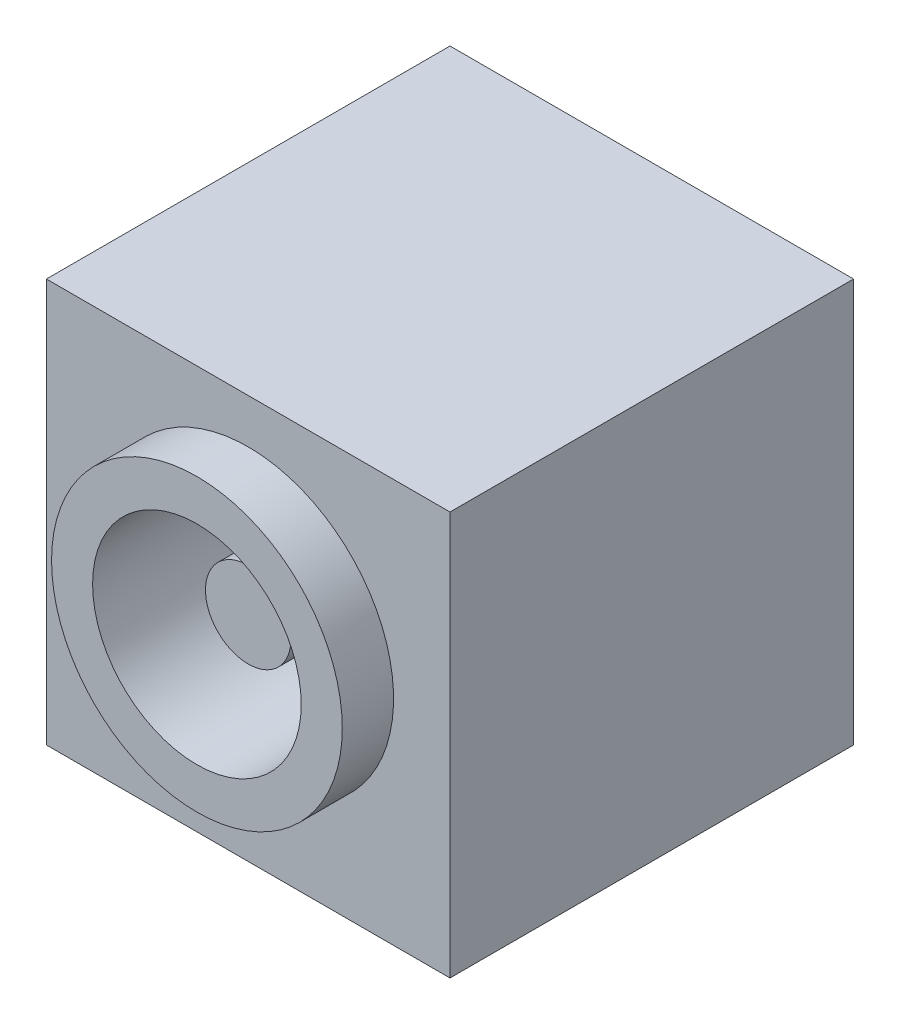
SolidWorks part; units mm, degrees
material "ABS"
ref_plane "Front Plane" through (0, 0, 0) normal (0, 0, 1) x (1, 0, 0)
ref_plane "Top Plane" through (0, 0, 0) normal (0, 1, 0) x (1, 0, 0)
ref_plane "Right Plane" through (0, 0, 0) normal (1, 0, 0) x (0, 0, -1)
sketch "Sketch1" plane through (0, 0, 0) normal (0, 1, 0) x (1, 0, 0)
  line L1 (0, 0) -> (11.8, 0)
  line L2 (0, 0) -> (0, 11.8)
  line L3 (0, 11.8) -> (11.8, 11.8)
  line L4 (11.8, 0) -> (11.8, 11.8)
  dimension "D1" = 11.8
  dimension "D2" = 11.8
extrude "Boss-Extrude1" add sketch "Sketch1" along normal blind 11.8
sketch "Sketch2" plane through (0, 0, 0) normal (0, 0, 1) x (1, 0, 0)
  line L0 (0, 0) -> (11.8, 0) construction
  line L2 (0, 11.8) -> (11.8, 11.8) construction
  line L3 (5.9, 11.8) -> (5.9, 3.3977) construction
  circle A0 centre (5.9, 6.25) radius 4.25
  point P2 (5.9, 0)
  dimension "D1" = 8.5
  dimension "D2" = 6.25
extrude "Boss-Extrude2" add sketch "Sketch2" along normal blind 1.5
sketch "Sketch3" plane through (0, 0, 1.5) normal (0, 0, 1) x (1, 0, 0)
  circle A0 centre (5.9, 6.25) radius 3.05
  circle A1 centre (5.9, 6.25) radius 4.25 construction
  dimension "D1" = 1.2
extrude "Cut-Extrude1" cut sketch "Sketch3" against normal blind 9.5
sketch "Sketch4" plane through (0, 0, -8) normal (0, 0, 1) x (1, 0, 0)
  circle A0 centre (5.9, 6.25) radius 1.25
  dimension "D1" = 2.5
extrude "Boss-Extrude3" add sketch "Sketch4" along normal blind 8
